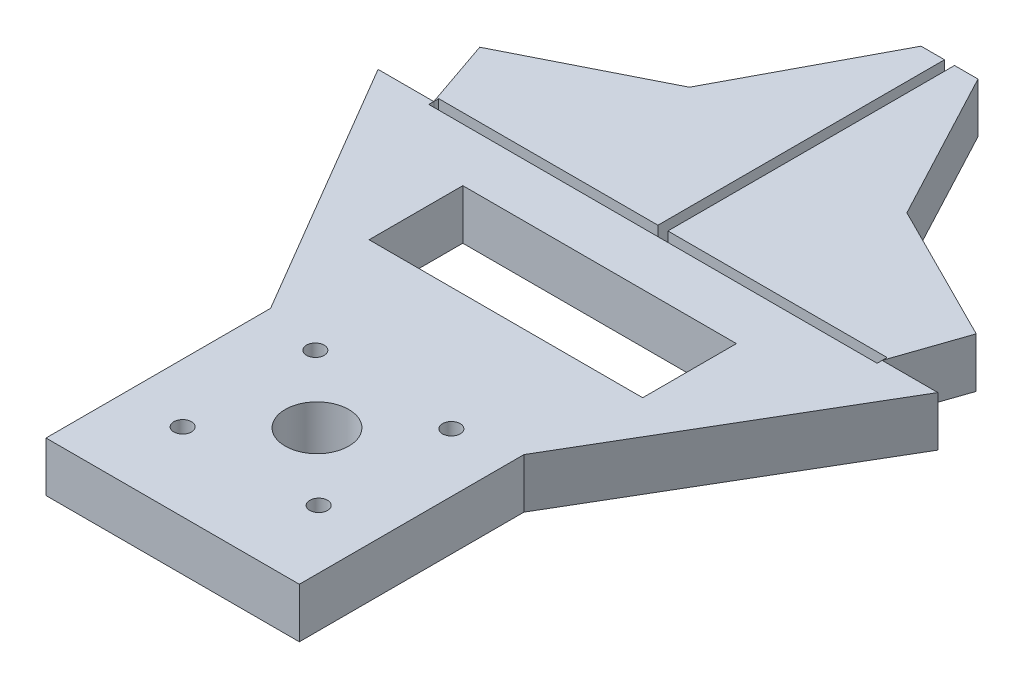
SolidWorks part; units mm, degrees
material "ABS"
ref_plane "Front Plane" through (0, 0, 0) normal (0, 0, 1) x (1, 0, 0)
ref_plane "Top Plane" through (0, 0, 0) normal (0, 1, 0) x (1, 0, 0)
ref_plane "Right Plane" through (0, 0, 0) normal (1, 0, 0) x (0, 0, -1)
sketch "Sketch1" plane through (0, 0, 0) normal (0, 1, 0) x (1, 0, 0)
  line L0 (5.709, 0) -> (-5.709, 0)
  line L1 (-5.709, 0) -> (-21.8095, -30.3557)
  line L2 (-21.8095, -30.3557) -> (-49.7782, -44.4231)
  line L3 (-49.7782, -44.4231) -> (-44.9535, -58.4708)
  line L4 (-44.9535, -58.4708) -> (44.9535, -58.4708)
  line L5 (0, -58.4708) -> (0, 0)
  line L6 (49.7782, -44.4231) -> (44.9535, -58.4708)
  line L7 (21.8095, -30.3557) -> (49.7782, -44.4231)
  line L8 (5.709, 0) -> (21.8095, -30.3557)
  line L9 (-44.9535, -58.4708) -> (44.9535, -58.4708)
  line L10 (56.1229, -58.4708) -> (25.4, -110.742)
  line L11 (25.4, -110.742) -> (25.4, -155.7768)
  line L12 (25.4, -155.7768) -> (-25.4, -155.7768)
  line L13 (-25.4, -155.7768) -> (-25.4, -110.742)
  line L14 (-25.4, -110.742) -> (-56.1229, -58.4708)
  line L15 (-56.1229, -58.4708) -> (-44.9535, -58.4708)
  line L16 (56.1229, -58.4708) -> (44.9535, -58.4708)
  line L17 (0, -155.7768) -> (0, -58.4708) construction
  point P18 (-56.1229, -58.4708)
  dimension "D1" = 58.4708
  dimension "D2" = 50.8
extrude "Boss-Extrude1" add sketch "Sketch1" along normal blind 10 contours L12 L17 L4 L15 L14 L13 | L17 L12 L11 L10 L16 L4 | L8 L0 L5 L4 L6 L7 | L4 L5 L0 L1 L2 L3
sketch "Sketch2" plane through (0, 10, 0) normal (0, 1, 0) x (1, 0, 0)
  line L0 (0, 0) -> (0, -58.4708) construction
  line L2 (-44.9535, -58.4708) -> (-1, -58.4708) construction
  line L3 (-1, 0) -> (-1, -57.4708)
  line L4 (-44.9535, -59.4708) -> (44.9535, -59.4708)
  line L5 (1, 0) -> (1, -57.4708)
  line L6 (-44.9535, -57.4708) -> (-1, -57.4708)
  line L7 (-1, 0) -> (1, 0)
  line L9 (-44.9535, -59.4708) -> (-44.9535, -57.4708)
  line L10 (44.9535, -59.4708) -> (44.9535, -57.4708)
  line L11 (1, -58.4708) -> (44.9535, -58.4708) construction
  line L12 (-44.9535, -58.4708) -> (44.9535, -58.4708) construction
  line L13 (-1, 0) -> (-1, -58.4708) construction
  line L14 (1, -57.4708) -> (44.9535, -57.4708)
  line L15 (-44.9535, -57.4708) -> (44.9535, -57.4708) construction
  line L16 (1, 0) -> (1, -58.4708) construction
  point P7 (0, -58.4708)
  dimension "D1" = 1
  dimension "D2" = 1
extrude "Cut-Extrude1" cut sketch "Sketch2" against normal blind 10
sketch "Sketch3" plane through (0, 10, 0) normal (0, 1, 0) x (1, 0, 0)
  line L0 (-13.6383, -113.5364) -> (-13.6383, -140.1371) construction
  line L1 (13.6383, -113.5364) -> (-13.6383, -140.1371) construction
  line L2 (-13.6383, -140.1371) -> (13.6383, -140.1371) construction
  line L3 (13.6383, -140.1371) -> (13.6383, -113.5364) construction
  line L4 (13.6383, -113.5364) -> (-13.6383, -113.5364) construction
  line L5 (-13.6383, -113.5364) -> (13.6383, -140.1371) construction
  line L6 (0, -126.8368) -> (-25.4, -126.8368) construction
  line L7 (-25.4, -155.7768) -> (-25.4, -110.742) construction
  line L8 (0, -126.8368) -> (25.4, -126.8368) construction
  line L9 (25.4, -110.742) -> (25.4, -155.7768) construction
  circle A0 centre (-13.6383, -140.1371) radius 1.78
  circle A1 centre (13.6383, -140.1371) radius 1.78
  circle A2 centre (13.6383, -113.5364) radius 1.78
  circle A3 centre (-13.6383, -113.5364) radius 1.78
  circle A4 centre (0, -126.8368) radius 6.3754
  dimension "D2" = 3.56
  dimension "D3" = 12.7508
  dimension "D1" = 38.1
extrude "Cut-Extrude2" cut sketch "Sketch3" against normal blind 10
sketch "Sketch4" plane through (0, 10, 0) normal (0, 1, 0) x (1, 0, 0)
  line L1 (27.432, -70.1653) -> (-27.432, -70.1653)
  line L2 (27.432, -70.1653) -> (27.432, -88.9613)
  line L3 (27.432, -88.9613) -> (-27.432, -88.9613)
  line L4 (-27.432, -70.1653) -> (-27.432, -88.9613)
  line L5 (27.432, -70.1653) -> (-27.432, -88.9613) construction
  line L6 (27.432, -88.9613) -> (-27.432, -70.1653) construction
  point P0 (0, -79.5633)
  point P5 (4.7242, -80.1431)
  point P6 (0, -79.9284)
  point P7 (-27.432, -79.5633)
  point P8 (0, -79.5633)
  dimension "D1" = 18.796
  dimension "D2" = 54.864
extrude "Cut-Extrude3" cut sketch "Sketch4" against normal blind 10
